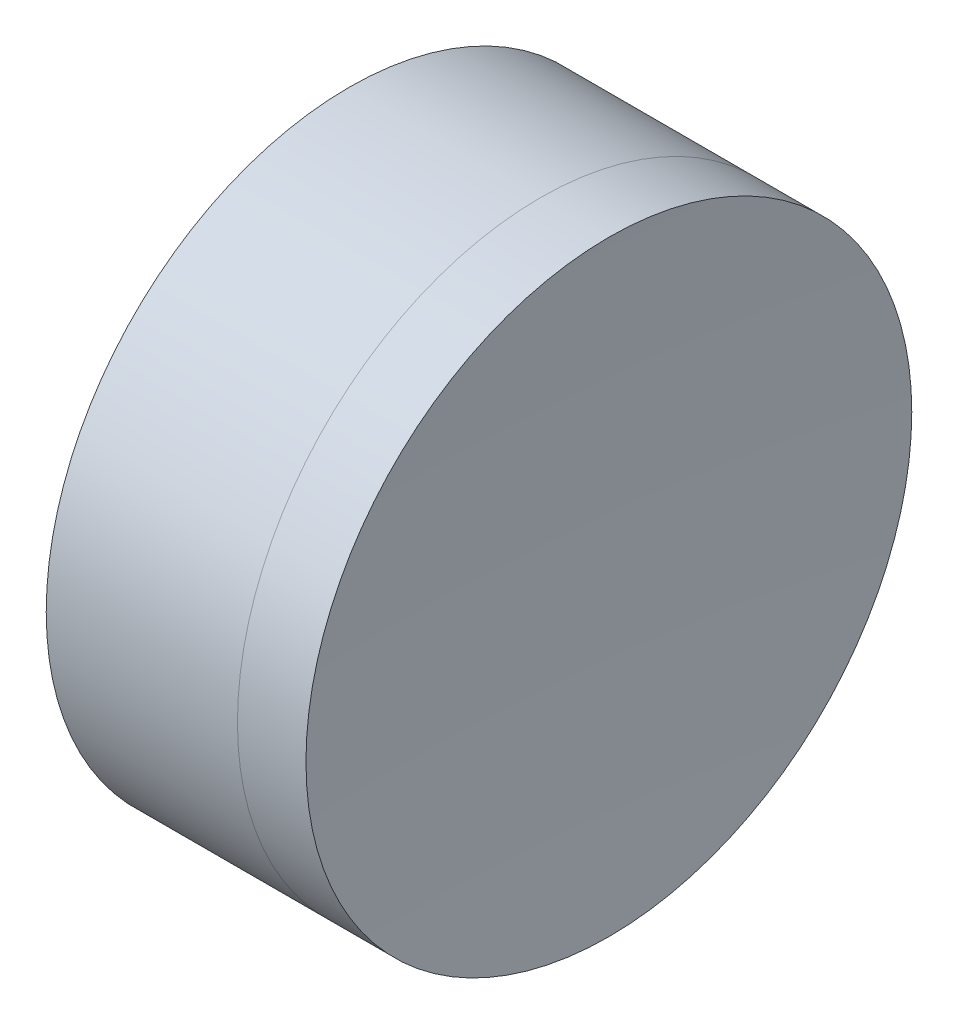
SolidWorks part; units mm, degrees
ref_plane "前视基准面" through (0, 0, 0) normal (0, 0, 1) x (1, 0, 0)
ref_plane "上视基准面" through (0, 0, 0) normal (0, 1, 0) x (1, 0, 0)
ref_plane "右视基准面" through (0, 0, 0) normal (1, 0, 0) x (0, 0, -1)
sketch "草图1" plane through (0, 0, 0) normal (0, 1, 0) x (1, 0, 0)
  line L0 (-0.8161, 0) -> (425.6391, 0) construction
  line L1 (228.0732, 6.35) -> (232.0824, 6.35)
  line L4 (228.0732, -6.35) -> (232.0824, -6.35)
  arc A0 (228.0732, -6.35) -> (228.0732, 6.35) centre (212.4115, 0) ccw
  arc A1 (232.0824, 6.35) -> (232.0824, -6.35) centre (247.3115, 0) ccw
  point P6 (229.3115, 0)
  point P8 (230.8115, 0)
  dimension "D3" = 6.35
  dimension "D4" = 1.5
  dimension "D1" = 16.9
  dimension "D5" = 16.5
  dimension "D2" = 6.35
revolve "旋转1" add sketch "草图1" angle 360 about L0
sketch "草图2" plane through (0, 0, 0) normal (0, 1, 0) x (1, 0, 0)
  line L2 (228.0732, 0) -> (234.9944, 0) construction
  line L3 (228.0732, -6.35) -> (228.0732, 6.35) construction
  line L6 (232.0824, 6.35) -> (233.5181, 6.35)
  line L7 (232.0824, -6.35) -> (233.5181, -6.35)
  arc A2 (232.0824, 6.35) -> (232.0824, -6.35) centre (247.3115, 0) ccw construction
  arc A3 (232.0824, 6.35) -> (232.0824, -6.35) centre (247.3115, 0) ccw
  arc A4 (233.5181, 6.35) -> (233.5181, -6.35) centre (331.0115, 0) ccw
  point P8 (230.8115, 0)
  point P9 (233.3115, 0)
  dimension "D1" = 2.5
  dimension "D2" = 97.7
revolve "旋转3" add sketch "草图2" angle 360 about L2
